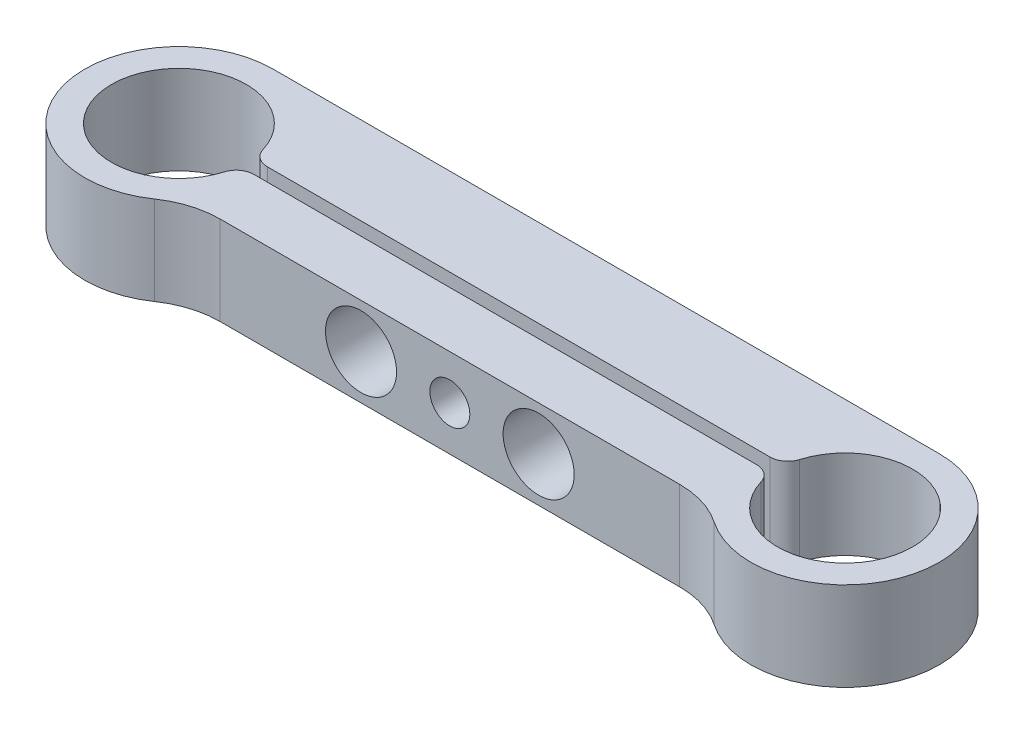
SolidWorks part; units mm, degrees
ref_plane "Спереди" through (0, 0, 0) normal (0, 0, 1) x (1, 0, 0)
ref_plane "Сверху" through (0, 0, 0) normal (0, 1, 0) x (1, 0, 0)
ref_plane "Справа" through (0, 0, 0) normal (1, 0, 0) x (0, 0, -1)
sketch "Эскиз1" plane through (0, 0, 0) normal (0, 1, 0) x (1, 0, 0)
  line L0 (0, 0) -> (75, 0) construction
  line L1 (67.0401, -7) -> (7.9599, -7)
  line L2 (0, 10.6) -> (75, 10.6)
  line L3 (7.5629, -0.75) -> (67.4371, -0.75)
  line L4 (7.5629, 0.75) -> (67.4371, 0.75)
  arc A0 (7.5629, 0.75) -> (7.5629, -0.75) centre (0, 0) ccw
  arc A1 (0, 10.6) -> (7.9599, -7) centre (0, 0) ccw
  arc A2 (67.4371, -0.75) -> (67.4371, 0.75) centre (75, 0) ccw
  arc A3 (67.0401, -7) -> (75, 10.6) centre (75, 0) ccw
  circle A5 centre (0, 0) radius 10.6 construction
  circle A6 centre (0, 0) radius 7.6 construction
  point P4 (7.1723, 2.1928)
  point P6 (10.0412, 3.0699)
  dimension "D1" = 15.2
  dimension "D4" = 7
  dimension "D3" = 75
  dimension "D5" = 1.5
  dimension "D2" = 3
extrude "Бобышка-Вытянуть1" add sketch "Эскиз1" along normal blind 10
sketch "Эскиз2" plane through (0, 0, 7) normal (0, 0, 1) x (1, 0, 0)
  line L0 (27.5, 5) -> (47.5, 5) construction
  line L1 (37.5, 10) -> (37.5, 0) construction
  line L2 (7.9599, 10) -> (67.0401, 10) construction
  line L3 (7.9599, 0) -> (67.0401, 0) construction
  point P8 (37.5, 5)
  dimension "D1" = 20
hole_wizard "Диаметр отверстия Ø8.0 (8)1" positions "Эскиз4" profile "Эскиз3" hole size "Ø8.0" standard "Ansi Metric" end condition up to next
sketch "Эскиз4" plane through (0, 0, 7) normal (0, 0, 1) x (1, 0, 0)
  point P0 (27.5, 5)
  point P6 (47.5, 5)
sketch "Эскиз3" plane through (27.5, 5, 7) normal (1, 0, 0) x (0, -1, 0)
  line L0 (0, 0) -> (0, 6.25)
  line L1 (0, 6.25) -> (4, 6.25)
  line L2 (4, 6.25) -> (4, 0)
  line L5 (4, 0) -> (0, 0)
  line L11 (0, -6.35) -> (0, 107.95) construction
  dimension "Диаметр сквозного отверстия" = 8
  dimension "Глубина сквозного отверстия" = 6.25
hole_wizard "Отверстие с зазором M41" positions "Эскиз6" profile "Эскиз5" hole size "M4" standard "Ansi Metric"
sketch "Эскиз6" plane through (0, 0, -0.75) normal (0, 0, 1) x (1, 0, 0)
  point P0 (47.5, 5)
  point P3 (27.5, 5)
sketch "Эскиз5" plane through (47.5, 5, -0.75) normal (1, 0, 0) x (0, -1, 0)
  line L0 (0, 0) -> (0, 12.3519)
  line L1 (0, 12.3519) -> (2.25, 11)
  line L2 (2.25, 11) -> (2.25, 0)
  line L5 (2.25, 0) -> (0, 0)
  line L10 (0, 12.3519) -> (-2.25, 11) construction
  line L11 (0, -6.35) -> (0, 107.95) construction
  dimension "Диаметр отверстия" = 4.5
  dimension "Глубина отверстия" = 11
  dimension "Угол заточки сверла" = 118
hole_wizard "Отверстие с зазором M42" positions "Эскиз8" profile "Эскиз7" hole size "M4" standard "Ansi Metric" end condition up to next
sketch "Эскиз8" plane through (0, 0, 7) normal (0, 0, 1) x (1, 0, 0)
  point P0 (37.5, 5)
sketch "Эскиз7" plane through (37.5, 5, 7) normal (1, 0, 0) x (0, -1, 0)
  line L0 (0, 0) -> (0, 6.25)
  line L1 (0, 6.25) -> (2.25, 6.25)
  line L2 (2.25, 6.25) -> (2.25, 0)
  line L5 (2.25, 0) -> (0, 0)
  line L11 (0, -6.35) -> (0, 107.95) construction
  dimension "Диаметр сквозного отверстия" = 4.5
  dimension "Глубина сквозного отверстия" = 6.25
hole_wizard "Отверстие обработанное метчиком M4x0.72" positions "Эскиз10" profile "Эскиз9" tap size "M4x0.7" standard "Ansi Metric" end condition through all
sketch "Эскиз10" plane through (0, 0, -0.75) normal (0, 0, 1) x (1, 0, 0)
  point P0 (37.5, 5)
sketch "Эскиз9" plane through (37.5, 5, -0.75) normal (1, 0, 0) x (0, -1, 0)
  line L0 (0, 0) -> (0, 9.85)
  line L1 (0, 9.85) -> (1.65, 9.85)
  line L2 (1.65, 9.85) -> (1.65, 0)
  line L5 (1.65, 0) -> (0, 0)
  line L11 (0, -6.35) -> (0, 107.95) construction
  dimension "Диаметр проходного сверла" = 3.3
  dimension "Глубина проходного сверла" = 9.85
cosmetic thread "Отверстие резьбы3" parameters "D2"=4
fillet "Скругление2" radius 10 2 edges at (7.9599, 5, 7) (67.0401, 5, 7)
fillet "Скругление3" radius 2 4 edges at (67.4371, 5, -0.75) (67.4371, 5, 0.75) (7.5629, 5, 0.75) (7.5629, 5, -0.75)
sketch "Эскиз11" plane through (0, 0, 0) normal (0, 1, 0) x (1, 0, 0)
  line L0 (75, 10.6) -> (0, 10.6) construction
  line L1 (-10.6, 16.2124) -> (-10.6, -17.96) construction
  arc A4 (0, 10.6) -> (5.9866, -8.7476) centre (0, 0) ccw construction
  point P0 (-10.6, 10.6)
